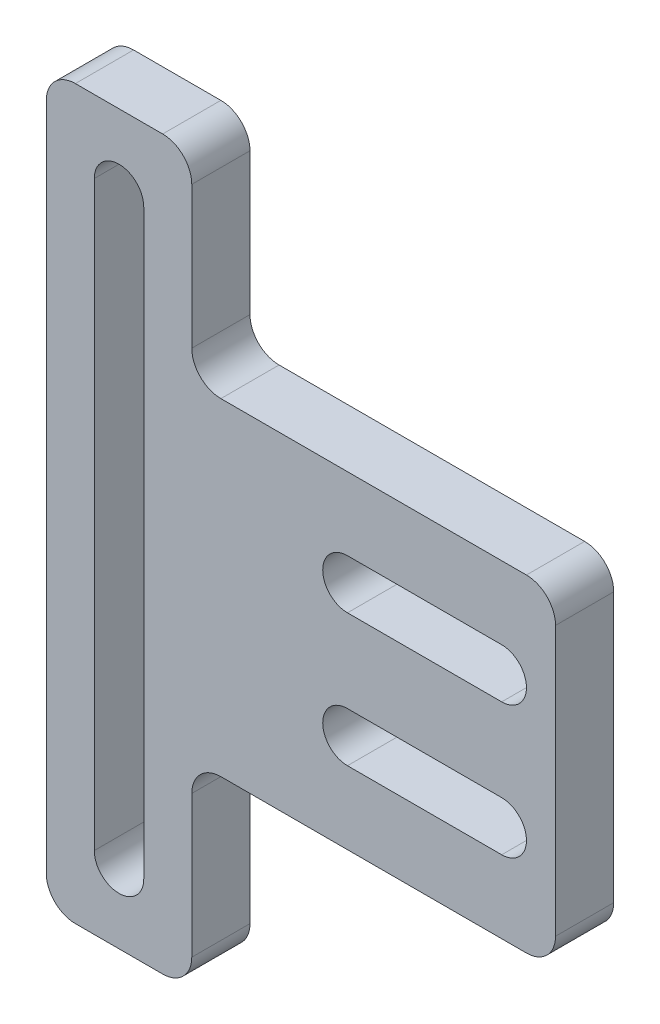
SolidWorks part; units mm, degrees
ref_plane "Plan de face" through (0, 0, 0) normal (0, 0, 1) x (1, 0, 0)
ref_plane "Plan de dessus" through (0, 0, 0) normal (0, 1, 0) x (1, 0, 0)
ref_plane "Plan de droite" through (0, 0, 0) normal (1, 0, 0) x (0, 0, -1)
sketch "Esquisse1" plane through (0, 0, 0) normal (0, 0, 1) x (1, 0, 0)
  line L0 (3.2, 4.55) -> (13.8, 4.55) construction
  line L1 (-17.5, -25) -> (17.5, -25) construction
  line L2 (-17.5, -25) -> (-17.5, 25)
  line L3 (-17.5, 25) -> (17.5, 25) construction
  line L4 (17.5, -25) -> (17.5, 25) construction
  line L5 (-17.5, -25) -> (17.5, 25) construction
  line L6 (-17.5, 25) -> (17.5, -25) construction
  line L7 (3.2, 6.25) -> (13.8, 6.25)
  line L8 (3.2, 2.85) -> (13.8, 2.85)
  line L9 (2.2, 0) -> (-2.2, 0) construction
  line L10 (3.2, -4.55) -> (13.8, -4.55) construction
  line L11 (3.2, -6.25) -> (13.8, -6.25)
  line L12 (3.2, -2.85) -> (13.8, -2.85)
  line L13 (-12.5, 25) -> (-12.5, -25) construction
  line L14 (-17.5, 25) -> (-7.5, 25)
  line L17 (17.5, 11.25) -> (-7.5, 11.25)
  line L18 (-7.5, 25) -> (-7.5, 11.25)
  line L20 (17.5, -11.25) -> (-7.5, -11.25)
  line L21 (-7.5, -25) -> (-7.5, -11.25)
  line L22 (-17.5, -25) -> (-7.5, -25)
  line L23 (17.5, -11.25) -> (17.5, 11.25)
  line L24 (-12.5, 20) -> (-12.5, -20) construction
  line L25 (-10.8, 20) -> (-10.8, -20)
  line L26 (-14.2, 20) -> (-14.2, -20)
  arc A0 (3.2, 6.25) -> (3.2, 2.85) centre (3.2, 4.55) ccw
  arc A1 (13.8, 2.85) -> (13.8, 6.25) centre (13.8, 4.55) ccw
  arc A2 (3.2, -6.25) -> (3.2, -2.85) centre (3.2, -4.55) cw
  arc A3 (13.8, -2.85) -> (13.8, -6.25) centre (13.8, -4.55) cw
  arc A6 (-10.8, 20) -> (-14.2, 20) centre (-12.5, 20) ccw
  arc A7 (-14.2, -20) -> (-10.8, -20) centre (-12.5, -20) ccw
  point P0 (0, 0)
  point P8 (8.5, 4.55)
  point P17 (8.5, -4.55)
  point P22 (8.5, 6.25)
  point P23 (1.5, 4.55)
  point P24 (15.5, 4.55)
  point P28 (0, 0)
  point P38 (-12.5, 0)
  dimension "D4" = 1.7
  dimension "D5" = 14
  dimension "D8" = 40
  dimension "D12" = 1.7
  dimension "D1" = 35
  dimension "D2" = 50
  dimension "D3" = 12.5
  dimension "D6" = 5
  dimension "D7" = 21
  dimension "D10" = 5
  dimension "D11" = 5
extrude "Boss.-Extru.1" add sketch "Esquisse1" along normal mid plane 4
fillet "Congé1" radius 2 8 edges at (-7.5, 25, 0) (17.5, 11.25, 0) (17.5, -11.25, 0) (-7.5, -11.25, 0) (-7.5, 11.25, 0) (-17.5, 25, 0) (-7.5, -25, 0) (-17.5, -25, 0)
